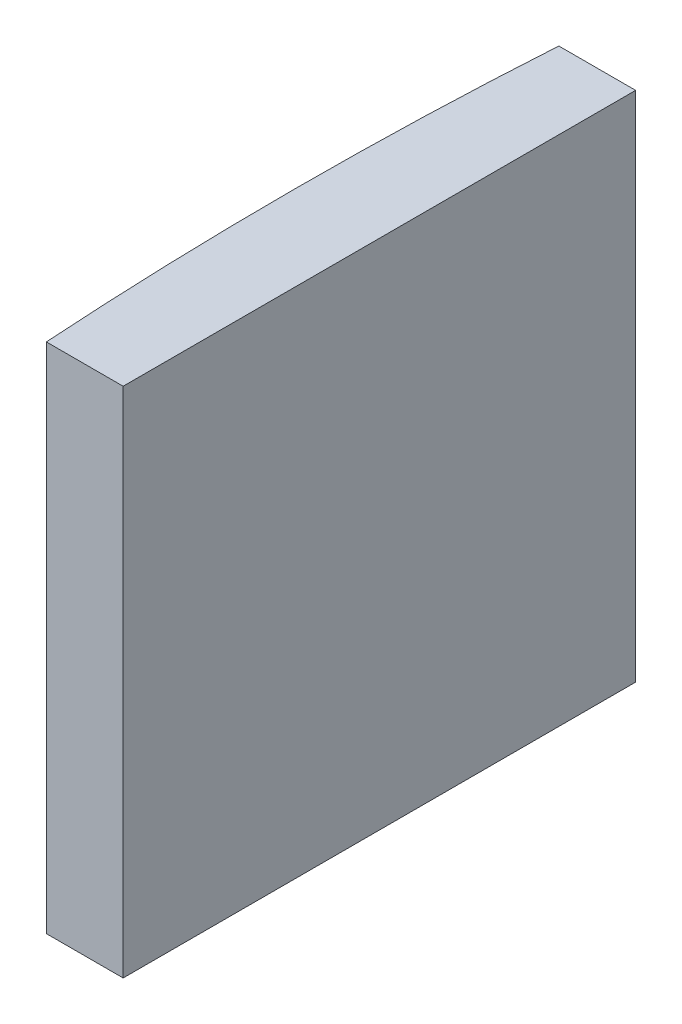
SolidWorks part; units mm, degrees
ref_plane "前视基准面" through (0, 0, 0) normal (0, 0, 1) x (1, 0, 0)
ref_plane "上视基准面" through (0, 0, 0) normal (0, 1, 0) x (1, 0, 0)
ref_plane "右视基准面" through (0, 0, 0) normal (1, 0, 0) x (0, 0, -1)
sketch "草图1" plane through (0, 0, 0) normal (0, 1, 0) x (1, 0, 0)
  line L0 (10.7432, 0) -> (-161.2447, 0) construction
  line L1 (-150.4221, 10) -> (-147.4248, 10)
  line L2 (-150.4221, -10) -> (-147.4248, -10)
  line L3 (-147.4248, 10) -> (-147.4248, -10)
  arc A0 (-150.4221, 10) -> (-150.4221, -10) centre (4.3552, 0) ccw
  point P2 (-161.2447, 0)
  point P19 (-150.7448, 0)
  point P20 (-147.4248, 0)
  dimension "D2" = 10
  dimension "D3" = 155.1
  dimension "D4" = 3.32
  dimension "D1" = 10
extrude "凸台-拉伸1" add sketch "草图1" along normal blind 20
